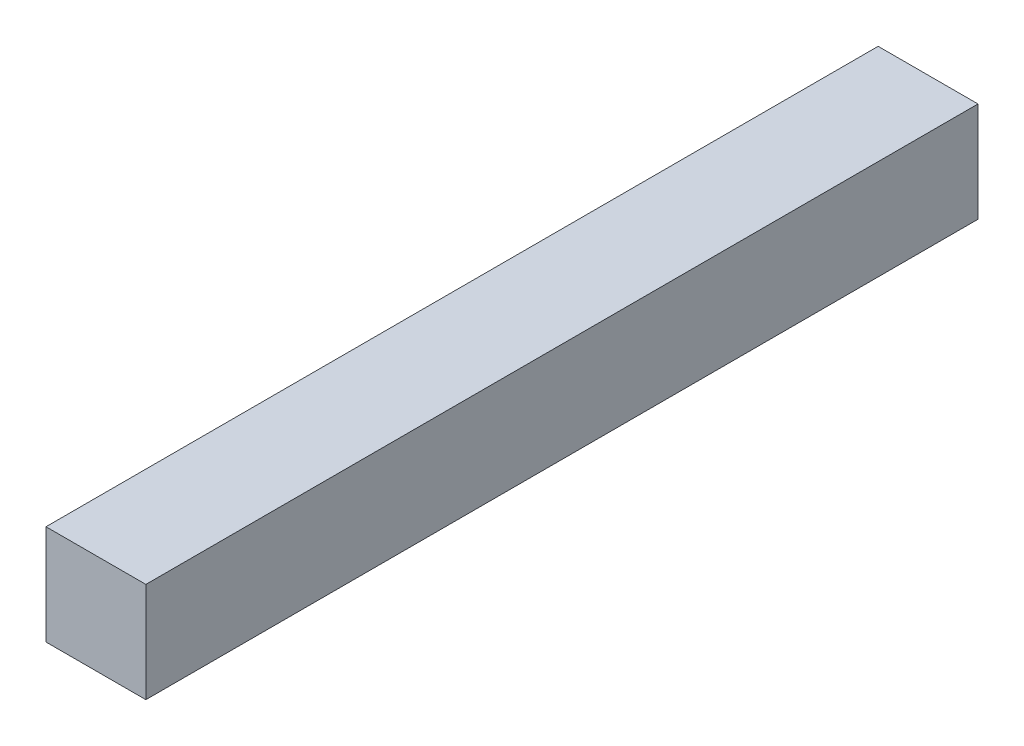
SolidWorks part; units mm, degrees
ref_plane "Piano frontale" through (0, 0, 0) normal (0, 0, 1) x (1, 0, 0)
ref_plane "Piano superiore" through (0, 0, 0) normal (0, 1, 0) x (1, 0, 0)
ref_plane "Piano destro" through (0, 0, 0) normal (1, 0, 0) x (0, 0, -1)
sketch "Schizzo1" plane through (0, 0, 0) normal (0, 0, 1) x (1, 0, 0)
  line L1 (0, 0) -> (3, 0)
  line L2 (0, 0) -> (0, -3)
  line L3 (0, -3) -> (3, -3)
  line L4 (3, 0) -> (3, -3)
  dimension "D1" = 3
  dimension "D2" = 3
extrude "Estrusione-Estrusione1" add sketch "Schizzo1" along normal blind 25
